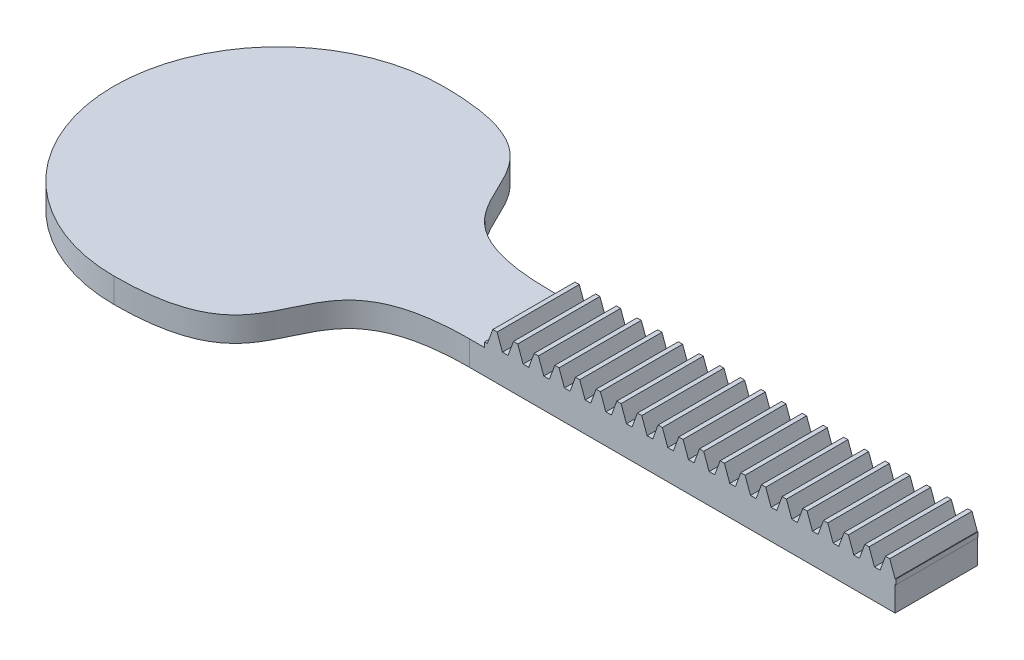
SolidWorks part; units mm, degrees
extrude "Blank" add sketch "BlankSke" against normal blind 100
sketch "BlankSke" plane through (0, 0, 0) normal (0, 0, 1) x (1, 0, 0)
  line L1 (0, 0) -> (500, 0)
  line L2 (0, 0) -> (0, 24)
  line L3 (0, 24) -> (500, 24)
  line L4 (500, 0) -> (500, 24)
  dimension "Length" = 500
  dimension "Blank_height" = 24
ref_plane "Plane1" through (0, 0, 0) normal (0, 0, 1) x (1, 0, 0)
ref_plane "Plane2" through (0, 0, 0) normal (0, 1, 0) x (1, 0, 0)
ref_plane "Plane3" through (0, 0, 0) normal (1, 0, 0) x (0, 0, -1)
sketch "HoldingSke" [suppressed] plane through (0, 0, 0) normal (0, 1, 0) x (1, 0, 0)
  line L0 (0, 0) -> (0.0174, 0.1238)
  line L1 (-15, 0) -> (100, 0) construction
  line L2 (0, 0) -> (-2.1039, 2.3779)
  line L3 (0, 0) -> (-11.863, 4.5341)
  line L4 (0, 0) -> (8.0624, 3.0949)
  line L5 (0, 0) -> (-23.7986, -8.8762)
  line L6 (0, 0) -> (-10.5278, -7.1032)
  line L9 (-71.009, 38.7566) -> (398.8373, 209.7667)
  line L10 (-76.2, 10.3779) -> (-60.2, 10.3779)
  line L11 (0, 0) -> (-100, 0)
  line L12 (-76.2, 101.6) -> (-75.945, 101.6)
  line L13 (24.9733, 27.94) -> (52.9518, 28.4284)
  line L14 (24.9733, 27.94) -> (24.9743, 27.94)
  line L15 (24.9733, 27.94) -> (100.4006, 29.5858)
  circle A0 centre (0, 0) radius 19.05
  circle A1 centre (0, 0) radius 8
  circle A2 centre (0, 0) radius 12.7
  dimension "MPH" = 16
  dimension "Diameter" = 38.1
  dimension "Num_teeth" = 21
  dimension "Pitch" = 0.125
  dimension "Show_teeth" = 998
  dimension "Thickness" = 12.7
  dimension "Ap" = 20
  dimension "Pitch_height" = 16
  dimension "Width" = 100
  dimension "Backlash" = 0.255
  dimension "Addendum_fac" = 1
  dimension "Dedendum_fac" = 1.25
  dimension "Clearance_fac" = 0.25
  dimension "Dedendum_add" = 0.001
  dimension "Length" = 500
  dimension "Module" = 8
sketch "TooCutSkeIll" plane through (0, 0, 0) normal (0, 0, 1) x (1, 0, 0)
  line L0 (-9.8833, 23.7894) -> (-3.8877, 7.3166)
  line L1 (-2.0074, 6) -> (2.0074, 6)
  line L2 (3.8877, 7.3166) -> (9.8833, 23.7894)
  line L3 (500, 24) -> (0, 24) construction
  line L4 (0, 0) -> (0, 64.897) construction
  line L5 (-13.208, 16) -> (12.954, 16) construction
  line L6 (0, 0) -> (500, 0) construction
  line L7 (7.0482, 16) -> (7.0482, 48.7463) construction
  line L8 (-7.0482, 16) -> (-7.0482, 48.7463) construction
  line L9 (10.184, 24) -> (10.184, 24.0254)
  line L10 (-10.184, 24) -> (-10.184, 24.0254)
  line L11 (-10.184, 24.0254) -> (10.184, 24.0254)
  arc A0 (2.0074, 6) -> (3.8877, 7.3166) centre (2.0074, 8.001) ccw
  arc A1 (-3.8877, 7.3166) -> (-2.0074, 6) centre (-2.0074, 8.001) ccw
  arc A2 (10.184, 24) -> (9.8833, 23.7894) centre (10.184, 23.68) ccw
  arc A3 (-9.8833, 23.7894) -> (-10.184, 24) centre (-10.184, 23.68) ccw
  dimension "Pitch_height" = 16
  dimension "Addendum_plus" = 8.0254
  dimension "Pressure_angle" = 20
  dimension "Gap_width" = 14.0964
  dimension "Dedendum" = 10
extrude "ToothCutIll" [suppressed] cut sketch "TooCutSkeIll" against normal through all
sketch "TooCutSkeSim" plane through (0, 0, 0) normal (0, 0, 1) x (1, 0, 0)
  line L0 (3.4085, 6) -> (-3.4085, 6)
  line L1 (9.9692, 24.0254) -> (3.4085, 6)
  line L2 (0, 17.4625) -> (0, 53.467) construction
  line L3 (9.9692, 24.0254) -> (-9.9692, 24.0254)
  line L6 (-9.9692, 24.0254) -> (-3.4085, 6)
  line L9 (-7.0482, 16) -> (7.0482, 16) construction
  line L10 (0, 0) -> (500, 0) construction
  line L11 (7.0482, 16) -> (7.0482, 53.467) construction
  line L12 (-7.0482, 16) -> (-7.0482, 53.467) construction
  dimension "Pitch_height" = 16
  dimension "Addendum_plus" = 8.0254
  dimension "Pressure_angle" = 20
  dimension "Gap_width" = 14.0964
  dimension "Dedendum" = 10
extrude "ToothCutSim" cut sketch "TooCutSkeSim" against normal through all
pattern_linear "TeethCuts" count 21 spacing 25.1327 along (1, 0, 0) of "ToothCutIll", "ToothCutSim"
sketch "Sketch1" plane through (0, 0, 0) normal (0, -1, 0) x (1, 0, 0)
  line L1 (499.2463, -100) -> (-300.7537, -100)
  line L2 (499.2463, -100) -> (499.2463, 0)
  line L3 (499.2463, 0) -> (-300.7537, 0)
  line L4 (-300.7537, -100) -> (-300.7537, 0)
  dimension "D1" = 800
extrude "Boss-Extrude1" add sketch "Sketch1" along normal blind 30
scale "Scale1" scale about centroid uniform scaling yes scale factor 0.25
sketch "Sketch3" plane through (0, -7.0725, 0) normal (0, 1, 0) x (1, 0, 0)
  line L0 (25.5712, 37.5) -> (25.5712, 62.5) construction
  line L1 (25.5712, 100) -> (25.5712, 0) construction
  line L2 (25.5712, 62.5) -> (100.7596, 62.5) construction
  line L3 (25.5712, 100) -> (96.2377, 62.5) construction
  line L4 (25.5712, 50) -> (100.7596, 50) construction
  line L5 (100.7596, 62.5) -> (100.7596, 37.5) construction
  line L6 (96.2377, 62.5) -> (25.5712, 62.5)
  line L7 (25.5712, 62.5) -> (25.5712, 37.5)
  line L8 (25.5712, 37.5) -> (96.2377, 37.5)
  arc A0 (25.5712, 100) -> (25.5712, 0) centre (25.5712, 50) ccw
  spline S0 degree 3 poles (25.5712, 100) (78.475, 100) (43.3338, 62.5) (96.2377, 62.5) knots 0 0 0 0 1 1 1 1
  spline S1 degree 3 poles (25.5712, 0) (78.475, 0) (43.3338, 37.5) (96.2377, 37.5) knots 0 0 0 0 1 1 1 1
  point P6 (60.9044, 81.25)
  dimension "D1" = 100
  dimension "D2" = 80
extrude "Boss-Extrude2" add sketch "Sketch3" against normal up to surface (7.5 mm away) up to face at (125.5712, -14.5725, -50)
ref_plane "Symmetry Plane" through (0, 0, -50) normal (0, 0, -1) x (-1, 0, 0)
equation "' \"Module@HoldingSke\" = 6.35"
equation "' \"Num_teeth@HoldingSke\" = 12"
equation "' \"Ap@HoldingSke\" =  20"
equation "' \"Ap@HoldingSke\" = 20"
equation "' \"Width@HoldingSke\" = 0.25 * 25.4"
equation "' \"Show_teeth@HoldingSke\" = 500"
equation "' \"Backlash@HoldingSke\" = 0.009 * 25.4"
equation "' \"Addendum_fac@HoldingSke\" = 1.0"
equation "' \"Dedendum_fac@HoldingSke\" = 1.25"
equation "' \"Dedendum_add@HoldingSke\" = 0.00005 * 25.4"
equation "' \"Clearance_fac@HoldingSke\" = 0.25"
equation "' \"Pitch_height@HoldingSke\" = 1 * 25.4"
equation "' \"Length@HoldingSke\" = 4.71 * 25.4"
equation "\"Pitch@HoldingSke\" = 1 / \"Module@HoldingSke\""
equation "\"MPH@HoldingSke\" = \"Dedendum_fac@HoldingSke\" / \"Pitch@HoldingSke\" + 2 * \"Dedendum_add@HoldingSke\" + 0.002 * 25.4"
equation "\"MPH@HoldingSke\"= ( ( sgn ( \"MPH@HoldingSke\" - \"Pitch_height@HoldingSke\" ) + 1 ) * ( \"MPH@HoldingSke\" - \"Pitch_height@HoldingSke\" ) ) / 2 + \"Pitch_height@HoldingSke\""
equation "\"Blank_height@BlankSke\" = \"Pitch_height@HoldingSke\" + \"Addendum_fac@HoldingSke\"  / \"Pitch@HoldingSke\" "
equation "\"Length@BlankSke\" =  \"Length@HoldingSke\""
equation "\"Face_width@Blank\" = \"Width@HoldingSke\""
equation "\"Pressure_angle@TooCutSkeIll\" = \"Ap@HoldingSke\""
equation "\"Addendum_plus@TooCutSkeIll\" =  \"Addendum_fac@HoldingSke\"  / \"Pitch@HoldingSke\" + 0.001 *25.4"
equation "\"Dedendum@TooCutSkeIll\" = \"Dedendum_fac@HoldingSke\"  / \"Pitch@HoldingSke\""
equation "\"Pitch_height@TooCutSkeIll\" =  \"MPH@HoldingSke\""
equation "\"Gap_width@TooCutSkeIll\" = 3.14159265 / 2 / \"Pitch@HoldingSke\" + 6 * \"Backlash@HoldingSke\""
equation "\"Pressure_angle@TooCutSkeSim\" = \"Ap@HoldingSke\""
equation "\"Addendum_plus@TooCutSkeSim\" =  \"Addendum_fac@HoldingSke\"  / \"Pitch@HoldingSke\" + 0.001 * 25.4"
equation "\"Dedendum@TooCutSkeSim\" = \"Dedendum_fac@HoldingSke\"  / \"Pitch@HoldingSke\""
equation "\"Pitch_height@TooCutSkeSim\" =  \"MPH@HoldingSke\""
equation "\"Gap_width@TooCutSkeSim\" = 3.14159265 / 2 / \"Pitch@HoldingSke\" + 6 * \"Backlash@HoldingSke\""
equation "\"Root_fillet@TooCutSkeIll\" = \"Clearance_fac@HoldingSke\" / \"Pitch@HoldingSke\" + \"Dedendum_add@HoldingSke\""
equation "\"Break_rad@TooCutSkeIll\" = 0.02 / \"Pitch@HoldingSke\" * 2"
equation "\"Linear_pitch@TeethCuts\" = 3.14159265 / \"Pitch@HoldingSke\""
equation "\"Num_teeth@HoldingSke\" = int( ( \"Length@HoldingSke\" + 0 ) / (3.14159265 / \"Pitch@HoldingSke\")) + 0.9999  + 1"
equation " \"Num_teeth@TeethCuts\" = int( \"Show_teeth@HoldingSke\" ) + 1"
equation " \"Num_teeth@TeethCuts\" = ((sgn( \"Num_teeth@TeethCuts\" - \"Num_teeth@HoldingSke\" )-1)*( \"Num_teeth@TeethCuts\" - \"Num_teeth@HoldingSke\" ))/-2+ \"Num_teeth@HoldingSke\""
equation " \"Num_teeth@TeethCuts\" = ((sgn( \"Num_teeth@TeethCuts\" - 2.0)+1)*( \"Num_teeth@TeethCuts\" - 2.0))/2 +2.0"
